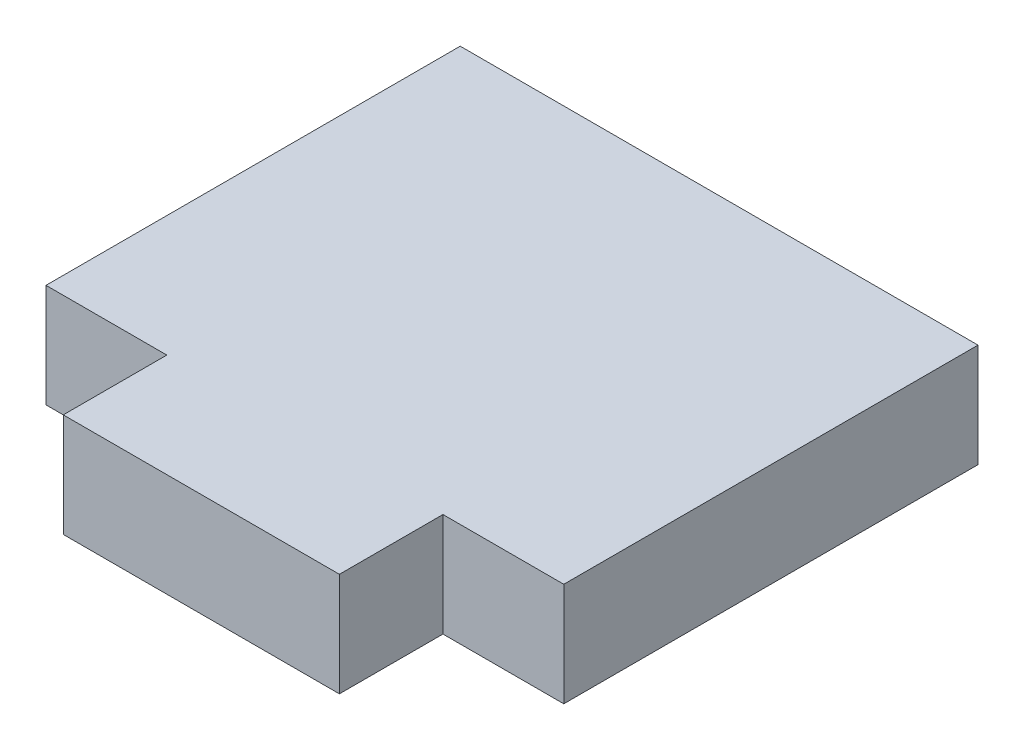
SolidWorks part; units mm, degrees
material "Acrylic (Medium-high impact)"
ref_plane "Plano frontal" through (0, 0, 0) normal (0, 0, 1) x (1, 0, 0)
ref_plane "Plano superior" through (0, 0, 0) normal (0, 1, 0) x (1, 0, 0)
ref_plane "Plano direito" through (0, 0, 0) normal (1, 0, 0) x (0, 0, -1)
sketch "Sketch6" plane through (0, 0, 0) normal (0, 1, 0) x (1, 0, 0)
  line L1 (-7.5, 6) -> (7.5, 6)
  line L2 (-7.5, 6) -> (-7.5, -6)
  line L3 (-7.5, -6) -> (7.5, -6)
  line L4 (7.5, 6) -> (7.5, -6)
  point P4 (0, 6)
  point P6 (-7.5, 0)
  dimension "D1" = 15
  dimension "D2" = 12
extrude "Boss-Extrude4" add sketch "Sketch6" along normal mid plane 3
sketch "Sketch8" plane through (0, 0, 0) normal (0, 1, 0) x (1, 0, 0)
  line L5 (-7.5, -6) -> (7.5, -6) construction
  line L6 (-4, -6) -> (4, -6)
  line L7 (-4, -6) -> (-4, -9)
  line L8 (-4, -9) -> (4, -9)
  line L9 (4, -6) -> (4, -9)
  point P14 (0, -6)
  dimension "D1" = 3
  dimension "D3" = 8
extrude "Boss-Extrude5" add sketch "Sketch8" along normal mid plane 3
